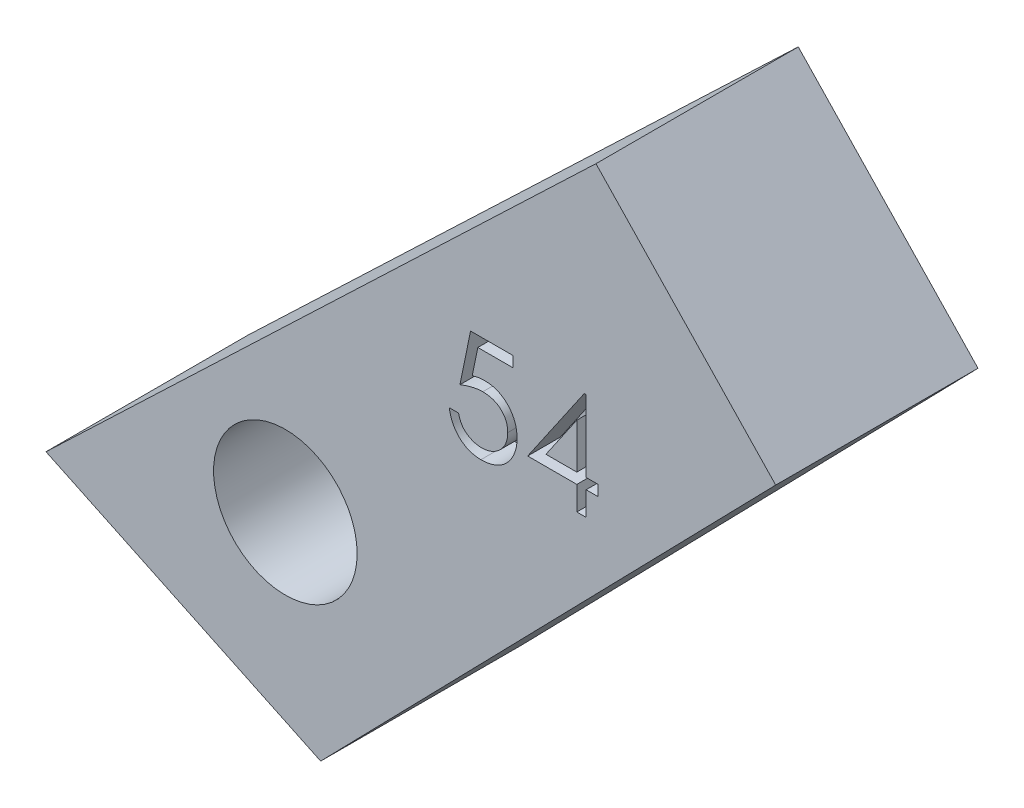
SolidWorks part; units mm, degrees
ref_plane "Front Plane" through (0, 0, 0) normal (0, 0, 1) x (1, 0, 0)
ref_plane "Top Plane" through (0, 0, 0) normal (0, 1, 0) x (1, 0, 0)
ref_plane "Right Plane" through (0, 0, 0) normal (1, 0, 0) x (0, 0, -1)
sketch "Sketch1" plane through (0, 0, 0) normal (0, 0, 1) x (-1, 0, 0)
  line L0 (-149.8064, 88.1094) -> (-144.2985, 82.3334)
  line L1 (-134.4358, 91.7384) -> (-127.4439, 98.4057)
  line L2 (-102.5471, 86.5653) -> (-91.0517, 81.0983)
  line L4 (-81.1984, 94.9837) -> (-74.9984, 94.9837)
  line L7 (-81.1984, 84.9837) -> (-74.9984, 84.9837)
  line L8 (-74.9984, 94.9837) -> (-74.9984, 84.9837)
  line L10 (-102.5385, 76.5687) -> (-81.1984, 84.9837)
  line L11 (-102.5471, 86.5653) -> (-81.1984, 94.9837)
  line L12 (-135.8612, 102.4088) -> (-102.5471, 86.5653)
  line L13 (-102.5385, 76.5687) -> (-134.4358, 91.7384)
  line L14 (-135.8612, 102.4088) -> (-149.8064, 88.1094)
  line L15 (-134.4358, 91.7384) -> (-149.8602, 77.0299)
  line L16 (-149.8602, 77.0299) -> (-173.8996, 100.1656)
  line L17 (-167.8618, 106.1938) -> (-149.8064, 88.1094)
  line L18 (-167.8618, 106.1938) -> (-173.8996, 100.1656)
  circle A1 centre (-134.7796, 96.3447) radius 2.2
  circle A2 centre (-168.0878, 100.0957) radius 2.2
  circle A3 centre (-149.935, 82.7336) radius 2.2
  circle A4 centre (-102.4484, 81.8835) radius 2.2
  point P3 (-149.935, 82.7336)
  point P25 (-102.5385, 76.5687)
  point P26 (-102.5471, 86.5653)
  point P29 (-135.8612, 102.4088)
  point P30 (-149.8064, 88.1094)
  point P35 (-149.8602, 77.0299)
  point P37 (-167.8618, 106.1938)
  point P38 (-173.8996, 100.1656)
  dimension "D2" = 10
  dimension "D3" = 6.2
extrude "Boss-Extrude1" add sketch "Sketch1" along normal blind 6.2 contours L15 L1 L12 L14 L0 A1
sketch "Sketch2" plane through (0, 0, 6.2) normal (0, 0, 1) x (1, 0, 0)
  text T0 "54"
extrude "Cut-Extrude1" cut sketch "Sketch2" against normal blind 1
